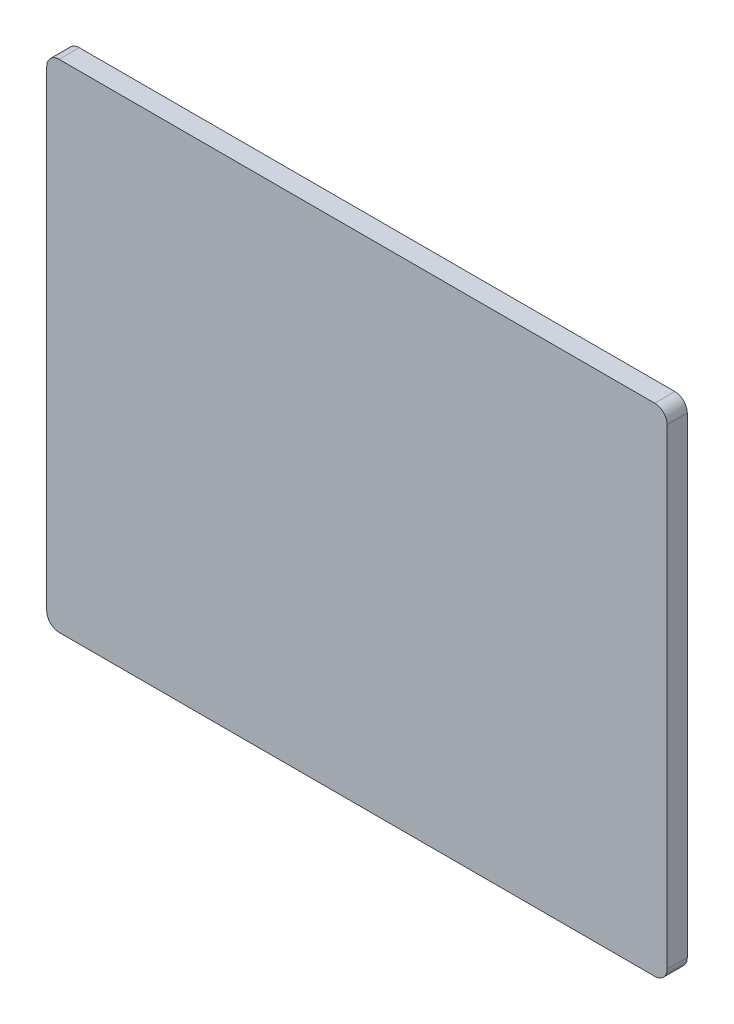
SolidWorks part; units mm, degrees
material "아크릴(내충격성)"
ref_plane "정면" through (0, 0, 0) normal (0, 0, 1) x (1, 0, 0)
ref_plane "윗면" through (0, 0, 0) normal (0, 1, 0) x (1, 0, 0)
ref_plane "우측면" through (0, 0, 0) normal (1, 0, 0) x (0, 0, -1)
ref_plane "평면1" through (0, 0, 13) normal (0, 0, 1) x (1, 0, 0)
sketch "스케치1" plane through (0, 0, 13) normal (0, 0, 1) x (1, 0, 0)
  line L0 (-202.723, -243.2676) -> (197.277, -243.2676)
  line L1 (197.277, -243.2676) -> (197.277, 246.7324)
  line L2 (197.277, 246.7324) -> (-202.723, 246.7324)
  line L3 (-202.723, 246.7324) -> (-202.723, -243.2676)
  line L5 (-202.723, 246.7324) -> (197.277, 246.7324)
  line L6 (-202.723, 246.7324) -> (-202.723, 76.7324)
  line L7 (-202.723, 76.7324) -> (197.277, 76.7324)
  line L8 (197.277, 246.7324) -> (197.277, 76.7324)
  dimension "D1" = 170
  dimension "D2" = 320
  dimension "D3" = 400
extrude "보스-돌출1" add sketch "스케치1" against normal blind 13 contours L7 L3 L0 L1
fillet "필렛1" radius 8 4 edges at (-202.723, -243.2676, 6.5) (197.277, -243.2676, 6.5) (197.277, 76.7324, 6.5) (-202.723, 76.7324, 6.5)
